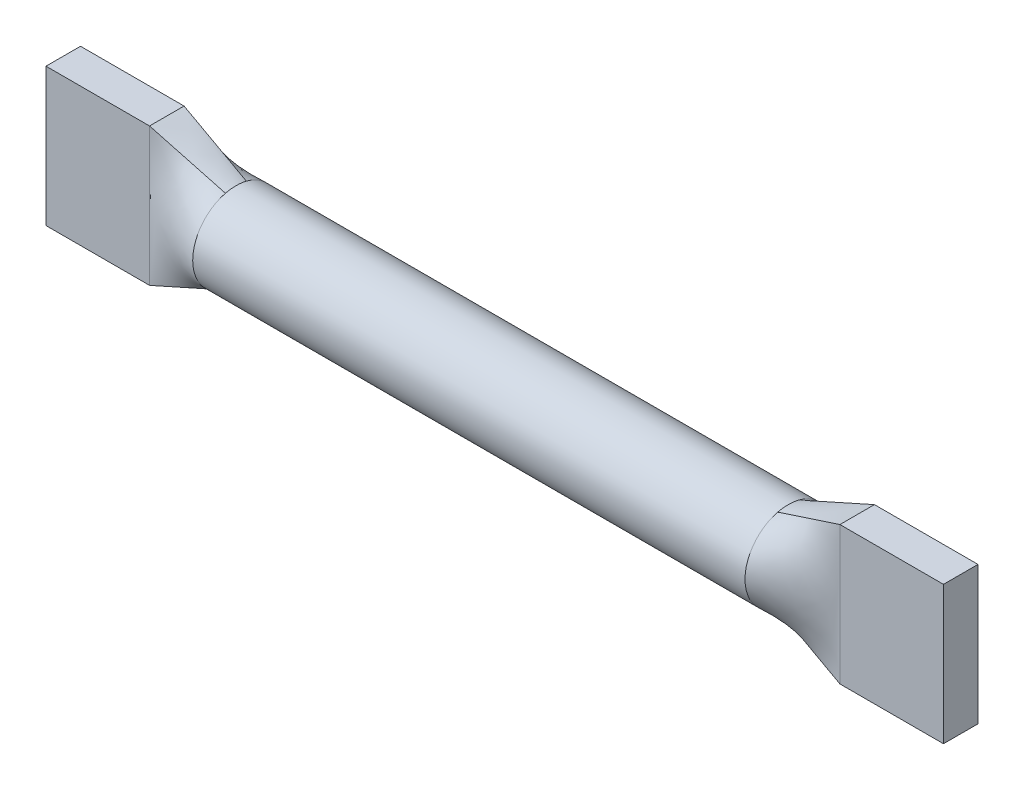
SolidWorks part; units mm, degrees
material "3.0517 (EN-AW 3003)"
ref_plane "Front Plane" through (0, 0, 0) normal (0, 0, 1) x (1, 0, 0)
ref_plane "Top Plane" through (0, 0, 0) normal (0, 1, 0) x (1, 0, 0)
ref_plane "Right Plane" through (0, 0, 0) normal (1, 0, 0) x (0, 0, -1)
sketch "Sketch1" plane through (0, 0, 0) normal (1, 0, 0) x (0, 0, -1)
  circle A0 centre (0, 0) radius 0.625
  dimension "D1" = 1.25
extrude "Boss-Extrude1" add sketch "Sketch1" along normal mid plane 8
ref_plane "Plane1" through (5, 0, 0) normal (1, 0, 0) x (0, 0, -1)
sketch "Sketch2" plane through (5, 0, 0) normal (1, 0, 0) x (0, 0, -1)
  line L1 (0.25, -1) -> (-0.25, -1)
  line L2 (0.25, -1) -> (0.25, 1)
  line L3 (0.25, 1) -> (-0.25, 1)
  line L4 (-0.25, -1) -> (-0.25, 1)
  line L5 (0.25, -1) -> (-0.25, 1) construction
  line L6 (0.25, 1) -> (-0.25, -1) construction
  point P0 (0, 0)
  dimension "D1" = 2
  dimension "D2" = 0.5
sketch "Sketch3" plane through (4, 0, 0) normal (1, 0, 0) x (0, 0, -1)
  circle A1 centre (0, 0) radius 0.625
  circle A2 centre (0, 0) radius 0.625
  dimension "D1" = 0
loft "Loft1" add profiles "Sketch2", "Sketch3"
sketch "Sketch4" plane through (5, 0, 0) normal (1, 0, 0) x (0, 0, -1)
  line L4 (-0.25, 1) -> (-0.25, -1)
  line L5 (-0.25, -1) -> (0.25, -1)
  line L6 (0.25, -1) -> (0.25, 1)
  line L7 (0.25, 1) -> (-0.25, 1)
  line L8 (-0.25, 1) -> (-0.25, -1)
  line L9 (-0.25, -1) -> (0.25, -1)
  line L10 (0.25, -1) -> (0.25, 1)
  line L11 (0.25, 1) -> (-0.25, 1)
  dimension "D1" = 0
extrude "Boss-Extrude2" add sketch "Sketch4" along normal blind 1.5
mirror "Mirror1" about plane through (0, 0, 0) normal (1, 0, 0) of "Boss-Extrude2", "Loft1"
